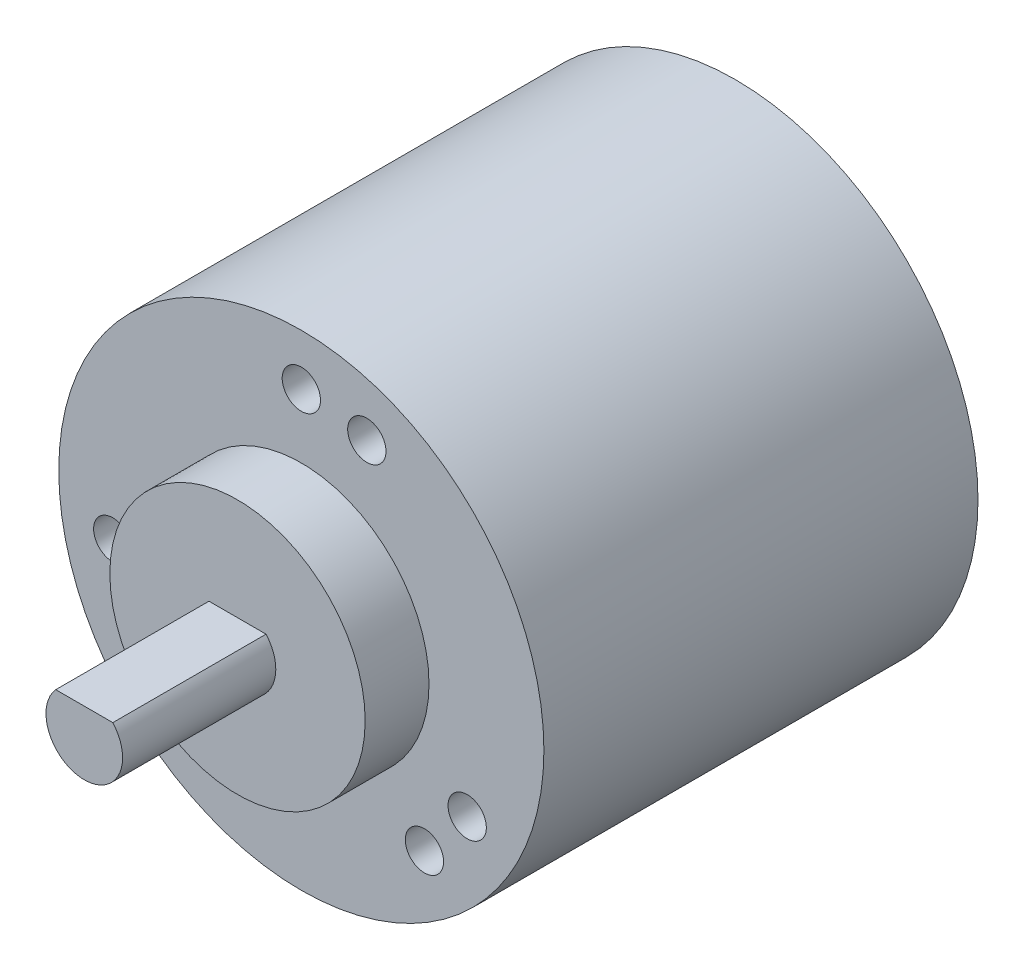
SolidWorks part; units mm, degrees
material "1060 Alloy"
ref_plane "Front Plane" through (0, 0, 0) normal (0, 0, 1) x (1, 0, 0)
ref_plane "Top Plane" through (0, 0, 0) normal (0, 1, 0) x (1, 0, 0)
ref_plane "Right Plane" through (0, 0, 0) normal (1, 0, 0) x (0, 0, -1)
sketch "Sketch1" plane through (0, 0, 0) normal (0, 0, 1) x (1, 0, 0)
  circle A0 centre (0, 0) radius 19
  dimension "D1" = 38
extrude "Boss-Extrude1" add sketch "Sketch1" along normal blind 34
sketch "Sketch2" plane through (0, 0, 34) normal (0, 0, 1) x (1, 0, 0)
  line L0 (0, 15) -> (0, 0) construction
  line L1 (0, 0) -> (5.1303, 14.0954) construction
  circle A0 centre (0, 0) radius 10
  circle A1 centre (0, 0) radius 15 construction
  circle A2 centre (0, 15) radius 1.5
  circle A3 centre (5.1303, 14.0954) radius 1.5
  circle A4 centre (9.6418, -11.4907) radius 1.5
  circle A5 centre (12.9904, -7.5) radius 1.5
  circle A6 centre (-14.7721, -2.6047) radius 1.5
  circle A7 centre (-12.9904, -7.5) radius 1.5
  point P18 (0, 0)
  dimension "D1" = 20
  dimension "D2" = 30
  dimension "D3" = 3
  dimension "D4" = 20
  dimension "D5" = 3
extrude "Cut-Extrude1" cut sketch "Sketch2" against normal blind 6 contours A7 | A6 | A2 | A3 | A5 | A4
sketch "Sketch3" plane through (0, 0, 34) normal (0, 0, 1) x (1, 0, 0)
  circle A0 centre (0, 0) radius 10
  dimension "D1" = 20
extrude "Boss-Extrude2" add sketch "Sketch3" along normal blind 5
sketch "Sketch4" plane through (0, 0, 39) normal (0, 0, 1) x (1, 0, 0)
  line L0 (2.2361, 2) -> (-2.2361, 2)
  circle A0 centre (0, 0) radius 3
  dimension "D1" = 6
  dimension "D2" = 2
extrude "Boss-Extrude3" add sketch "Sketch4" along normal blind 12 contours L0 A0
